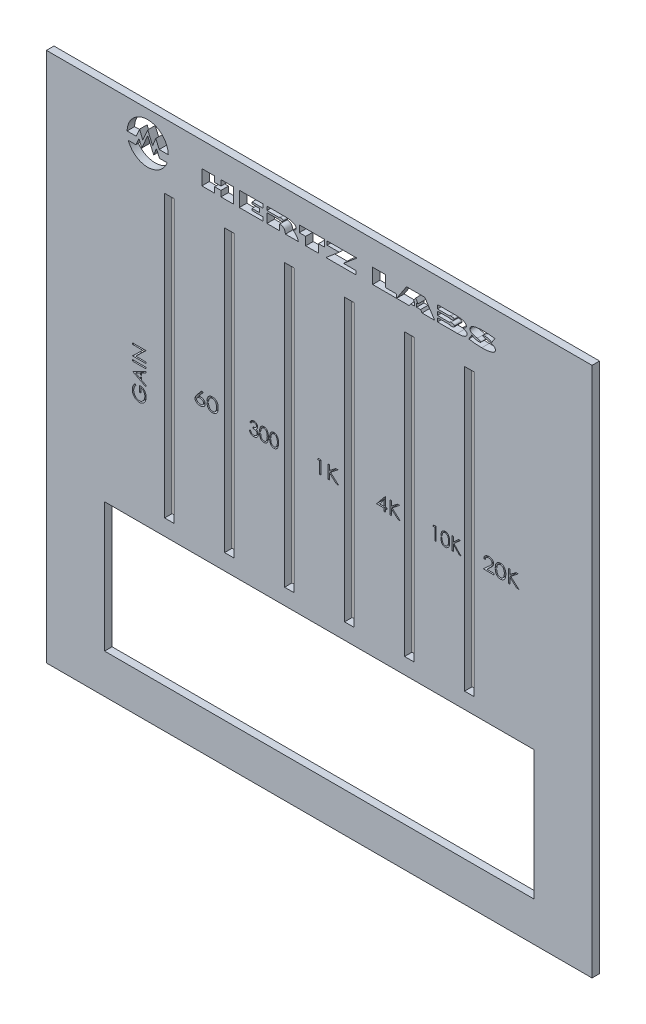
SolidWorks part; units mm, degrees
ref_plane "Front Plane" through (0, 0, 0) normal (0, 0, 1) x (1, 0, 0)
ref_plane "Top Plane" through (0, 0, 0) normal (0, 1, 0) x (1, 0, 0)
ref_plane "Right Plane" through (0, 0, 0) normal (1, 0, 0) x (0, 0, -1)
sketch "Sketch1" plane through (0, 0, 0) normal (0, 0, 1) x (1, 0, 0)
  line L1 (72.75, -70.75) -> (-72.75, -70.75)
  line L2 (72.75, -70.75) -> (72.75, 70.75)
  line L3 (72.75, 70.75) -> (-72.75, 70.75)
  line L4 (-72.75, -70.75) -> (-72.75, 70.75)
  line L5 (72.75, -70.75) -> (-72.75, 70.75) construction
  line L6 (72.75, 70.75) -> (-72.75, -70.75) construction
  point P0 (0, 0)
  dimension "D1" = 141.5
  dimension "D2" = 145.5
extrude "Boss-Extrude1" add sketch "Sketch1" along normal blind 2
sketch "Sketch2" plane through (0, 0, 2) normal (0, 0, 1) x (1, 0, 0)
  line L0 (-72.75, 70.75) -> (-72.75, -70.75) construction
  line L1 (-57.25, -60.25) -> (57.25, -60.25)
  line L2 (-57.25, -60.25) -> (-57.25, -25.75)
  line L3 (-57.25, -25.75) -> (57.25, -25.75)
  line L4 (57.25, -60.25) -> (57.25, -25.75)
  line L5 (72.75, -70.75) -> (72.75, 70.75) construction
  line L6 (-72.75, -70.75) -> (72.75, -70.75) construction
  line L7 (72.75, 70.75) -> (-72.75, 70.75) construction
  line L8 (-40, -3.9255) -> (-40, 57.7871) construction
  line L9 (-24, -3.9255) -> (-24, 57.7871) construction
  line L10 (-8, 57.7871) -> (-8, -3.9255) construction
  line L11 (0, -1.1) -> (0, 1.1) construction
  line L12 (-38.75, -21.5) -> (-41.25, -21.5)
  line L13 (-38.75, -21.5) -> (-38.75, 53.5)
  line L14 (-38.75, 53.5) -> (-41.25, 53.5)
  line L15 (-41.25, -21.5) -> (-41.25, 53.5)
  line L16 (-38.75, -21.5) -> (-41.25, 53.5) construction
  line L17 (-38.75, 53.5) -> (-41.25, -21.5) construction
  line L18 (-22.75, -21.5) -> (-25.25, -21.5)
  line L19 (-22.75, -21.5) -> (-22.75, 53.5)
  line L20 (-22.75, 53.5) -> (-25.25, 53.5)
  line L21 (-25.25, -21.5) -> (-25.25, 53.5)
  line L22 (-22.75, -21.5) -> (-25.25, 53.5) construction
  line L23 (-22.75, 53.5) -> (-25.25, -21.5) construction
  line L24 (-6.75, -21.5) -> (-9.25, -21.5)
  line L25 (-6.75, -21.5) -> (-6.75, 53.5)
  line L26 (-6.75, 53.5) -> (-9.25, 53.5)
  line L27 (-9.25, -21.5) -> (-9.25, 53.5)
  line L28 (-6.75, -21.5) -> (-9.25, 53.5) construction
  line L29 (-6.75, 53.5) -> (-9.25, -21.5) construction
  line L30 (6.75, 53.5) -> (9.25, 53.5)
  line L31 (9.25, -21.5) -> (9.25, 53.5)
  line L32 (6.75, -21.5) -> (9.25, -21.5)
  line L33 (6.75, -21.5) -> (6.75, 53.5)
  line L34 (22.75, 53.5) -> (25.25, 53.5)
  line L35 (25.25, -21.5) -> (25.25, 53.5)
  line L36 (22.75, -21.5) -> (25.25, -21.5)
  line L37 (22.75, -21.5) -> (22.75, 53.5)
  line L38 (38.75, 53.5) -> (41.25, 53.5)
  line L39 (41.25, -21.5) -> (41.25, 53.5)
  line L40 (38.75, -21.5) -> (41.25, -21.5)
  line L41 (38.75, -21.5) -> (38.75, 53.5)
  point P18 (-40, 16)
  point P23 (-24, 16)
  point P28 (-8, 16)
  dimension "D1" = 15.5
  dimension "D2" = 15.5
  dimension "D3" = 10.5
  dimension "D4" = 96.5
  dimension "D5" = 32.75
  dimension "D6" = 16
  dimension "D7" = 16
  dimension "D8" = 2.5
  dimension "D9" = 75
  dimension "D10" = 17.25
  dimension "D11" = 75
  dimension "D12" = 2.5
  dimension "D13" = 17.25
  dimension "D14" = 75
  dimension "D15" = 2.5
  dimension "D16" = 17.25
extrude "Cut-Extrude1" cut sketch "Sketch2" against normal blind 2
sketch "Sketch3" plane through (0, 0, 2) normal (0, 0, 1) x (1, 0, 0)
  line L0 (-46.537, 60.1618) -> (47.1821, 60.1618) construction
  text T0 "HERTZ LABS" font "Gill Sans Ultra Bold" height 4
extrude "Cut-Extrude2" cut sketch "Sketch3" against normal blind 2
sketch "Sketch4" plane through (0, 0, 2) normal (0, 0, 1) x (1, 0, 0)
  line L0 (-10.5679, 63.1618) -> (-13.9679, 63.1618)
  line L3 (-10.5679, 63.3118) -> (-10.5679, 62.5618) construction
  line L4 (-13.9679, 60.1618) -> (-13.9679, 64.1618) construction
  line L5 (-13.9679, 63.1618) -> (-13.9679, 62.6618)
  line L6 (-13.9679, 62.6618) -> (-10.5679, 62.6618)
  line L7 (-10.5679, 62.6618) -> (-10.5679, 63.1618)
  line L8 (25.4524, 60.7618) -> (25.4524, 61.7618)
  line L9 (27.0227, 60.7618) -> (24.3946, 60.7618) construction
  line L10 (25.0524, 61.7618) -> (26.3626, 61.7618) construction
  line L11 (25.4524, 61.7618) -> (25.9524, 61.7618)
  line L12 (25.9524, 61.7618) -> (25.9524, 60.7618)
  line L13 (25.9524, 60.7618) -> (25.4524, 60.7618)
  line L14 (34.9321, 63.1618) -> (31.5321, 63.1618)
  line L15 (34.9321, 63.3118) -> (34.9321, 62.5618) construction
  line L16 (31.5321, 60.1618) -> (31.5321, 64.1618) construction
  line L17 (31.5321, 63.1618) -> (31.5321, 62.6618)
  line L18 (31.5321, 62.6618) -> (34.9321, 62.6618)
  line L19 (34.9321, 62.6618) -> (34.9321, 63.1618)
  line L20 (34.9321, 61.6618) -> (31.5321, 61.6618)
  line L21 (34.9321, 61.8618) -> (34.9321, 61.0118) construction
  line L22 (31.5321, 61.6618) -> (31.5321, 61.1618)
  line L23 (31.5321, 61.1618) -> (34.9321, 61.1618)
  line L24 (34.9321, 61.1618) -> (34.9321, 61.6618)
  line L25 (31.5321, 64.1618) -> (36.2852, 64.1618) construction
  line L26 (36.8305, 60.1618) -> (31.5321, 60.1618) construction
  line L27 (-13.9679, 64.1618) -> (-8.957, 64.1618) construction
  dimension "D1" = 3.4
  dimension "D2" = 0.5
  dimension "D3" = 1
  dimension "D4" = 0.5
  dimension "D5" = 1
  dimension "D6" = 0.5
  dimension "D7" = 0.4
  dimension "D8" = 0.5
  dimension "D9" = 1
extrude "Boss-Extrude2" add sketch "Sketch4" against normal blind 2
sketch "Sketch5" plane through (0, 0, 2) normal (0, 0, 1) x (1, 0, 0)
  line L0 (-72.75, 70.75) -> (-72.75, -70.75) construction
  line L1 (72.75, 70.75) -> (-72.75, 70.75) construction
  line L2 (-51.2485, 62.8803) -> (-48.8137, 62.8803)
  line L3 (-48.8137, 62.8803) -> (-47.9043, 64.9798)
  line L4 (-47.9043, 64.9798) -> (-47.0636, 62.8542)
  line L5 (-47.0636, 62.8542) -> (-45.75, 65.8868)
  line L6 (-45.75, 69.0971) -> (-45.75, 56.4077) construction
  line L7 (-50.9225, 60.8803) -> (-48.8917, 60.8803)
  line L8 (-48.8917, 60.8803) -> (-48.0818, 62.75)
  line L9 (-48.0818, 62.75) -> (-47.3423, 60.8803)
  line L10 (-47.3423, 60.8803) -> (-45.75, 64.5564)
  line L11 (-40.5775, 60.8803) -> (-42.6083, 60.8803)
  line L12 (-42.6083, 60.8803) -> (-43.4182, 62.75)
  line L13 (-43.4182, 62.75) -> (-44.1577, 60.8803)
  line L14 (-44.1577, 60.8803) -> (-45.75, 64.5564)
  line L15 (-44.4364, 62.8542) -> (-45.75, 65.8868)
  line L16 (-43.5957, 64.9798) -> (-44.4364, 62.8542)
  line L17 (-42.6863, 62.8803) -> (-43.5957, 64.9798)
  line L18 (-40.2515, 62.8803) -> (-42.6863, 62.8803)
  arc A0 (-50.9225, 60.8803) -> (-40.5775, 60.8803) centre (-45.75, 62.75) ccw
  arc A1 (-40.2515, 62.8803) -> (-51.2485, 62.8803) centre (-45.75, 62.75) ccw
  dimension "D1" = 11
  dimension "D2" = 27
  dimension "D3" = 8
  dimension "D4" = 2
  dimension "D5" = 0
  dimension "D6" = 0
  dimension "D7" = 360
extrude "Cut-Extrude3" cut sketch "Sketch5" against normal blind 2
sketch "Sketch7" plane through (0, 0, 2) normal (0, 0, 1) x (1, 0, 0)
  line L0 (-34.0617, 9.25) -> (-26.7208, 9.25) construction
  line L1 (-19.38, 9.25) -> (-10.6797, 9.25) construction
  line L2 (-2.931, 9.25) -> (5.2255, 9.25) construction
  line L3 (13.9257, 9.25) -> (21.6744, 9.25) construction
  line L4 (29.0152, 9.25) -> (37.8514, 9.25) construction
  line L5 (43.561, 9.25) -> (56.6702, 9.25) construction
  line L6 (-46.25, 1.5274) -> (-46.25, 38.0957) construction
  line L7 (-41.25, 53.5) -> (-41.25, -21.5) construction
  line L8 (57.25, -25.75) -> (-57.25, -25.75) construction
  text T0 "60" font "Century Gothic" height 3.5
  text T1 "300" font "Century Gothic" height 3.5
  text T2 "1K" font "Century Gothic" height 3.5
  text T3 "4K" font "Century Gothic" height 3.5
  text T4 "10K" font "Century Gothic" height 3.5
  text T5 "20K" font "Century Gothic" height 3.5
  text T6 "GAIN" font "Century Gothic" height 3.5
  dimension "D1" = 5
  dimension "D2" = 35
extrude "Cut-Extrude4" cut sketch "Sketch7" against normal blind 2
sketch "Sketch8" plane through (0, 0, 2) normal (0, 0, 1) x (1, 0, 0)
  line L0 (-47.7308, 8.3128) -> (-47.3718, 8.3128)
  line L1 (-47.7308, 7.4399) -> (-47.7308, 8.7384) construction
  line L2 (-47.3718, 8.9172) -> (-47.3718, 7.2556) construction
  line L3 (-47.3718, 8.3128) -> (-47.3718, 7.907)
  line L4 (-47.3718, 7.907) -> (-47.7308, 7.907)
  line L5 (-47.7308, 7.907) -> (-47.7308, 8.3128)
  line L6 (-15.9287, 11.1102) -> (-15.6148, 11.1102)
  line L7 (-15.6148, 11.1102) -> (-15.6111, 10.7758)
  line L8 (-15.6111, 10.7758) -> (-15.9258, 10.7758)
  line L9 (-15.9258, 10.7758) -> (-15.9287, 11.1102)
  line L10 (-13.2364, 11.1102) -> (-12.9225, 11.1102)
  line L11 (-12.9225, 11.1102) -> (-12.92, 10.8036)
  line L12 (-12.92, 10.8036) -> (-13.2345, 10.8036)
  line L13 (-13.2345, 10.8036) -> (-13.2364, 11.1102)
  line L14 (-29.9472, 11.2049) -> (-29.4983, 11.2049)
  line L15 (-29.4983, 11.2049) -> (-29.5006, 10.8534)
  line L16 (-29.5006, 10.8534) -> (-29.9495, 10.8534)
  line L17 (-29.9495, 10.8534) -> (-29.9472, 11.2049)
  line L18 (32.4311, 11.326) -> (32.7462, 11.326)
  line L19 (32.7462, 11.326) -> (32.7363, 10.943)
  line L20 (32.7363, 10.943) -> (32.4223, 10.943)
  line L21 (32.4223, 10.943) -> (32.4311, 11.326)
  line L22 (46.9306, 11.2049) -> (47.3344, 11.2049)
  line L23 (47.3344, 11.2049) -> (47.3323, 10.8611)
  line L24 (47.3323, 10.8611) -> (46.9283, 10.8611)
  line L25 (46.9283, 10.8611) -> (46.9306, 11.2049)
  spline S0 degree 3 poles (-15.9297, 10.9986) (-15.9294, 11.0547) (-15.9287, 11.1637) (-15.9217, 11.3224) (-15.9099, 11.4714) (-15.8937, 11.6106) (-15.8741, 11.7399) (-15.8479, 11.8591) (-15.8181, 11.9688) (-15.7835, 12.0693) (-15.7445, 12.1618) (-15.7021, 12.2483) (-15.6545, 12.3284) (-15.6046, 12.4035) (-15.5502, 12.4724) (-15.4929, 12.5361) (-15.4304, 12.593) (-15.365, 12.6448) (-15.296, 12.6903) (-15.2253, 12.7303) (-15.1526, 12.7645) (-15.0775, 12.7914) (-15.0008, 12.8136) (-14.9222, 12.8288) (-14.8416, 12.8384) (-14.7871, 12.8393) (-14.7595, 12.8397) knots 0 0 0 0 0.068595 0.133246 0.194313 0.251279 0.304513 0.354235 0.400481 0.443411 0.484015 0.523252 0.561042 0.5979 0.633518 0.668314 0.702496 0.736685 0.770293 0.803437 0.835913 0.86846 0.900847 0.933467 0.966258 1 1 1 1 construction
  spline S1 degree 3 poles (-14.749, 12.4808) (-14.7877, 12.4787) (-14.8652, 12.4747) (-14.9797, 12.446) (-15.0894, 12.396) (-15.1766, 12.341) (-15.2435, 12.2887) (-15.2906, 12.2433) (-15.3347, 12.1936) (-15.3754, 12.1392) (-15.4135, 12.0808) (-15.4485, 12.0178) (-15.48, 11.95) (-15.5091, 11.8773) (-15.5346, 11.7978) (-15.5557, 11.71) (-15.5752, 11.6135) (-15.589, 11.5078) (-15.6013, 11.3935) (-15.6091, 11.2702) (-15.6153, 11.1382) (-15.6155, 11.047) (-15.6156, 11) knots 0 0 0 0 0.060387 0.120883 0.182755 0.247811 0.281299 0.315088 0.349702 0.384857 0.420966 0.458511 0.497175 0.537602 0.580503 0.627468 0.678388 0.733983 0.793747 0.857714 0.926698 1 1 1 1 construction
  spline S2 degree 3 poles (-15.6156, 11) (-15.6155, 10.9533) (-15.6153, 10.8625) (-15.6092, 10.7307) (-15.601, 10.6077) (-15.5903, 10.4935) (-15.5745, 10.3883) (-15.5568, 10.2915) (-15.5353, 10.2037) (-15.5098, 10.1241) (-15.4807, 10.0514) (-15.449, 9.9838) (-15.415, 9.9205) (-15.3768, 9.8619) (-15.3353, 9.808) (-15.2913, 9.7578) (-15.2433, 9.713) (-15.1768, 9.6593) (-15.089, 9.6038) (-14.9784, 9.5554) (-14.8647, 9.525) (-14.7875, 9.5212) (-14.749, 9.5192) knots 0 0 0 0 0.072951 0.141584 0.205926 0.265301 0.320597 0.371817 0.41879 0.461699 0.502134 0.540804 0.578181 0.614297 0.649678 0.684299 0.718359 0.752081 0.817652 0.879722 0.939966 1 1 1 1 construction
  spline S3 degree 3 poles (-14.7595, 9.1603) (-14.7871, 9.1607) (-14.8416, 9.1616) (-14.9222, 9.1712) (-15.0005, 9.1865) (-15.0768, 9.2079) (-15.1515, 9.2341) (-15.2236, 9.2682) (-15.2939, 9.3076) (-15.3622, 9.3524) (-15.4272, 9.4037) (-15.4893, 9.4605) (-15.5469, 9.5241) (-15.6006, 9.5936) (-15.6515, 9.6682) (-15.6984, 9.7492) (-15.7418, 9.836) (-15.7814, 9.9293) (-15.8166, 10.0305) (-15.8476, 10.1406) (-15.8721, 10.2608) (-15.8931, 10.3899) (-15.9101, 10.5285) (-15.9216, 10.6769) (-15.9288, 10.8347) (-15.9294, 10.943) (-15.9297, 10.9986) knots 0 0 0 0 0.033787 0.066622 0.099285 0.131361 0.163585 0.196104 0.228902 0.262158 0.295991 0.330218 0.36506 0.400951 0.43762 0.475708 0.515381 0.556414 0.599765 0.646424 0.696431 0.749782 0.806573 0.867436 0.931887 1 1 1 1 construction
  spline S4 degree 3 poles (-13.2374, 10.9986) (-13.2371, 11.0547) (-13.2364, 11.1637) (-13.2294, 11.3224) (-13.2176, 11.4714) (-13.2014, 11.6106) (-13.1818, 11.7399) (-13.1556, 11.8591) (-13.1258, 11.9688) (-13.0912, 12.0693) (-13.0522, 12.1618) (-13.0098, 12.2483) (-12.9622, 12.3284) (-12.9123, 12.4035) (-12.8578, 12.4724) (-12.8005, 12.5361) (-12.7381, 12.593) (-12.6727, 12.6448) (-12.6037, 12.6903) (-12.533, 12.7303) (-12.4603, 12.7645) (-12.3852, 12.7914) (-12.3085, 12.8136) (-12.2299, 12.8288) (-12.1493, 12.8384) (-12.0948, 12.8393) (-12.0672, 12.8397) knots 0 0 0 0 0.068595 0.133246 0.194313 0.251279 0.304513 0.354235 0.400481 0.443411 0.484015 0.523252 0.561042 0.5979 0.633518 0.668314 0.702496 0.736685 0.770293 0.803437 0.835913 0.86846 0.900847 0.933467 0.966258 1 1 1 1 construction
  spline S5 degree 3 poles (-12.0567, 12.4808) (-12.0954, 12.4787) (-12.1729, 12.4747) (-12.2874, 12.446) (-12.3971, 12.396) (-12.4843, 12.341) (-12.5512, 12.2887) (-12.5983, 12.2433) (-12.6424, 12.1936) (-12.6831, 12.1392) (-12.7212, 12.0808) (-12.7561, 12.0178) (-12.7877, 11.95) (-12.8167, 11.8773) (-12.8423, 11.7978) (-12.8634, 11.71) (-12.8829, 11.6135) (-12.8967, 11.5078) (-12.909, 11.3935) (-12.9168, 11.2702) (-12.923, 11.1382) (-12.9232, 11.047) (-12.9233, 11) knots 0 0 0 0 0.060387 0.120883 0.182755 0.247811 0.281299 0.315088 0.349702 0.384857 0.420966 0.458511 0.497175 0.537602 0.580503 0.627468 0.678388 0.733983 0.793747 0.857714 0.926698 1 1 1 1 construction
  spline S6 degree 3 poles (-12.9233, 11) (-12.9232, 10.9533) (-12.9229, 10.8625) (-12.9169, 10.7307) (-12.9086, 10.6077) (-12.898, 10.4935) (-12.8822, 10.3883) (-12.8645, 10.2915) (-12.8429, 10.2037) (-12.8174, 10.1241) (-12.7884, 10.0514) (-12.7567, 9.9838) (-12.7226, 9.9205) (-12.6845, 9.8619) (-12.643, 9.808) (-12.599, 9.7578) (-12.551, 9.713) (-12.4845, 9.6593) (-12.3967, 9.6038) (-12.286, 9.5554) (-12.1724, 9.525) (-12.0952, 9.5212) (-12.0567, 9.5192) knots 0 0 0 0 0.072951 0.141584 0.205926 0.265301 0.320597 0.371817 0.41879 0.461699 0.502134 0.540804 0.578181 0.614297 0.649678 0.684299 0.718359 0.752081 0.817652 0.879722 0.939966 1 1 1 1 construction
  spline S7 degree 3 poles (-12.0672, 9.1603) (-12.0948, 9.1607) (-12.1493, 9.1616) (-12.2299, 9.1712) (-12.3082, 9.1865) (-12.3845, 9.2079) (-12.4592, 9.2341) (-12.5313, 9.2682) (-12.6016, 9.3076) (-12.6699, 9.3524) (-12.7349, 9.4037) (-12.797, 9.4605) (-12.8546, 9.5241) (-12.9083, 9.5936) (-12.9592, 9.6682) (-13.0061, 9.7492) (-13.0495, 9.836) (-13.0891, 9.9293) (-13.1243, 10.0305) (-13.1553, 10.1406) (-13.1798, 10.2608) (-13.2008, 10.3899) (-13.2177, 10.5285) (-13.2293, 10.6769) (-13.2364, 10.8347) (-13.2371, 10.943) (-13.2374, 10.9986) knots 0 0 0 0 0.033787 0.066622 0.099285 0.131361 0.163585 0.196104 0.228902 0.262158 0.295991 0.330218 0.36506 0.400951 0.43762 0.475708 0.515381 0.556414 0.599765 0.646424 0.696431 0.749782 0.806573 0.867436 0.931887 1 1 1 1 construction
  spline S8 degree 3 poles (-29.9516, 10.9986) (-29.9512, 11.0547) (-29.9503, 11.1637) (-29.9408, 11.3225) (-29.9265, 11.4716) (-29.9062, 11.6108) (-29.8808, 11.7402) (-29.8484, 11.8596) (-29.811, 11.9696) (-29.7662, 12.0697) (-29.7167, 12.1623) (-29.6629, 12.2488) (-29.6034, 12.329) (-29.54, 12.4043) (-29.4708, 12.4729) (-29.3979, 12.5369) (-29.3187, 12.5931) (-29.2363, 12.6455) (-29.1493, 12.6904) (-29.0603, 12.7307) (-28.9686, 12.7647) (-28.874, 12.7916) (-28.7771, 12.8136) (-28.6778, 12.8289) (-28.5759, 12.8383) (-28.5071, 12.8393) (-28.4722, 12.8397) knots 0 0 0 0 0.062652 0.121739 0.177604 0.229836 0.278824 0.324793 0.367881 0.408429 0.447198 0.485074 0.522035 0.558698 0.594873 0.630771 0.666849 0.703204 0.739747 0.776081 0.812252 0.84893 0.885848 0.923096 0.961095 1 1 1 1 construction
  spline S9 degree 3 poles (-28.4582, 12.4808) (-28.5051, 12.4788) (-28.598, 12.4749) (-28.7355, 12.446) (-28.8677, 12.3969) (-28.9731, 12.3416) (-29.0534, 12.2888) (-29.1103, 12.2437) (-29.1636, 12.1941) (-29.2126, 12.1394) (-29.2596, 12.0817) (-29.3003, 12.0177) (-29.3395, 11.9506) (-29.3738, 11.8775) (-29.4055, 11.7983) (-29.4305, 11.7102) (-29.4534, 11.6137) (-29.4709, 11.5079) (-29.4861, 11.3936) (-29.4951, 11.2703) (-29.5018, 11.1382) (-29.5025, 11.047) (-29.5029, 11) knots 0 0 0 0 0.06843 0.135704 0.204056 0.273826 0.309041 0.344276 0.379774 0.415293 0.451486 0.488217 0.52598 0.56491 0.605982 0.650476 0.698495 0.750792 0.806886 0.866807 0.931388 1 1 1 1 construction
  spline S10 degree 3 poles (-29.5029, 11) (-29.5025, 10.9532) (-29.5018, 10.8625) (-29.4952, 10.7307) (-29.4859, 10.6076) (-29.4718, 10.4934) (-29.4539, 10.388) (-29.4314, 10.2914) (-29.406, 10.2033) (-29.3754, 10.1237) (-29.3407, 10.0511) (-29.3028, 9.9832) (-29.2607, 9.9203) (-29.2149, 9.8615) (-29.1649, 9.8077) (-29.1117, 9.7574) (-29.0538, 9.7127) (-28.9731, 9.6588) (-28.8669, 9.6031) (-28.7338, 9.5551) (-28.5972, 9.525) (-28.5046, 9.5211) (-28.4582, 9.5192) knots 0 0 0 0 0.068273 0.132516 0.192779 0.248494 0.300456 0.348809 0.393305 0.434254 0.473186 0.510782 0.547702 0.583685 0.619435 0.654935 0.690439 0.726129 0.796665 0.864903 0.932249 1 1 1 1 construction
  spline S11 degree 3 poles (-28.4722, 9.1603) (-28.5071, 9.1607) (-28.5759, 9.1617) (-28.6778, 9.171) (-28.7768, 9.1865) (-28.8732, 9.2077) (-28.9675, 9.2339) (-29.0586, 9.268) (-29.1472, 9.3075) (-29.2335, 9.3518) (-29.3155, 9.4033) (-29.3937, 9.4599) (-29.4669, 9.5235) (-29.5353, 9.5929) (-29.5997, 9.6675) (-29.6586, 9.7487) (-29.7132, 9.8355) (-29.7634, 9.9288) (-29.8089, 10.0297) (-29.8472, 10.1403) (-29.879, 10.2604) (-29.9055, 10.3896) (-29.9267, 10.5284) (-29.9408, 10.6768) (-29.9503, 10.8346) (-29.9512, 10.943) (-29.9516, 10.9986) knots 0 0 0 0 0.038955 0.077002 0.114298 0.150951 0.187352 0.223569 0.259604 0.295841 0.331882 0.367795 0.403739 0.440145 0.476656 0.513875 0.55216 0.591332 0.632276 0.675753 0.722032 0.771134 0.823213 0.87889 0.937791 1 1 1 1 construction
  spline S12 degree 3 poles (32.4219, 10.9986) (32.4223, 11.0547) (32.4229, 11.1637) (32.43, 11.3224) (32.4418, 11.4714) (32.4579, 11.6106) (32.4775, 11.7399) (32.5038, 11.8591) (32.5336, 11.9688) (32.5681, 12.0693) (32.6071, 12.1618) (32.6496, 12.2483) (32.6971, 12.3284) (32.7471, 12.4035) (32.8015, 12.4724) (32.8588, 12.5361) (32.9212, 12.593) (32.9866, 12.6448) (33.0557, 12.6903) (33.1263, 12.7303) (33.1991, 12.7645) (33.2741, 12.7914) (33.3508, 12.8136) (33.4294, 12.8288) (33.5101, 12.8384) (33.5645, 12.8393) (33.5921, 12.8397) knots 0 0 0 0 0.068595 0.133246 0.194313 0.251279 0.304513 0.354235 0.400481 0.443411 0.484015 0.523252 0.561042 0.5979 0.633518 0.668314 0.702496 0.736685 0.770293 0.803437 0.835913 0.86846 0.900847 0.933467 0.966258 1 1 1 1 construction
  spline S13 degree 3 poles (33.6026, 12.4808) (33.5639, 12.4787) (33.4864, 12.4747) (33.372, 12.446) (33.2623, 12.396) (33.175, 12.341) (33.1082, 12.2887) (33.0611, 12.2433) (33.0169, 12.1936) (32.9763, 12.1392) (32.9382, 12.0808) (32.9032, 12.0178) (32.8717, 11.95) (32.8426, 11.8773) (32.817, 11.7978) (32.7959, 11.71) (32.7764, 11.6135) (32.7627, 11.5078) (32.7504, 11.3935) (32.7425, 11.2702) (32.7364, 11.1382) (32.7362, 11.047) (32.736, 11) knots 0 0 0 0 0.060387 0.120883 0.182755 0.247811 0.281299 0.315088 0.349702 0.384857 0.420966 0.458511 0.497175 0.537602 0.580503 0.627468 0.678388 0.733983 0.793747 0.857714 0.926698 1 1 1 1 construction
  spline S14 degree 3 poles (32.736, 11) (32.7362, 10.9533) (32.7364, 10.8625) (32.7425, 10.7307) (32.7507, 10.6077) (32.7613, 10.4935) (32.7771, 10.3883) (32.7949, 10.2915) (32.8164, 10.2037) (32.8419, 10.1241) (32.8709, 10.0514) (32.9026, 9.9838) (32.9367, 9.9205) (32.9748, 9.8619) (33.0163, 9.808) (33.0603, 9.7578) (33.1084, 9.713) (33.1749, 9.6593) (33.2627, 9.6038) (33.3733, 9.5554) (33.487, 9.525) (33.5641, 9.5212) (33.6026, 9.5192) knots 0 0 0 0 0.072951 0.141584 0.205926 0.265301 0.320597 0.371817 0.41879 0.461699 0.502134 0.540804 0.578181 0.614297 0.649678 0.684299 0.718359 0.752081 0.817652 0.879722 0.939966 1 1 1 1 construction
  spline S15 degree 3 poles (33.5921, 9.1603) (33.5645, 9.1607) (33.5101, 9.1616) (33.4294, 9.1712) (33.3511, 9.1865) (33.2748, 9.2079) (33.2001, 9.2341) (33.128, 9.2682) (33.0578, 9.3076) (32.9895, 9.3524) (32.9245, 9.4037) (32.8624, 9.4605) (32.8047, 9.5241) (32.7511, 9.5936) (32.7001, 9.6682) (32.6532, 9.7492) (32.6099, 9.836) (32.5702, 9.9293) (32.5351, 10.0305) (32.504, 10.1406) (32.4795, 10.2608) (32.4585, 10.3899) (32.4416, 10.5285) (32.43, 10.6769) (32.4229, 10.8347) (32.4223, 10.943) (32.4219, 10.9986) knots 0 0 0 0 0.033787 0.066622 0.099285 0.131361 0.163585 0.196104 0.228902 0.262158 0.295991 0.330218 0.36506 0.400951 0.43762 0.475708 0.515381 0.556414 0.599765 0.646424 0.696431 0.749782 0.806573 0.867436 0.931887 1 1 1 1 construction
  spline S16 degree 3 poles (46.9264, 10.9986) (46.9268, 11.0547) (46.9278, 11.1637) (46.9367, 11.3225) (46.9491, 11.4716) (46.9691, 11.6107) (46.9932, 11.74) (47.0232, 11.8595) (47.0587, 11.9693) (47.1004, 12.0697) (47.1473, 12.162) (47.1974, 12.2487) (47.2535, 12.329) (47.3134, 12.404) (47.3783, 12.4729) (47.4469, 12.5366) (47.5212, 12.5931) (47.5986, 12.6452) (47.6803, 12.6905) (47.7643, 12.7306) (47.8507, 12.7644) (47.9396, 12.7917) (48.0307, 12.8136) (48.1242, 12.8289) (48.22, 12.8383) (48.2846, 12.8393) (48.3174, 12.8397) knots 0 0 0 0 0.064278 0.124884 0.18215 0.2357 0.285857 0.332815 0.376766 0.417944 0.457225 0.495391 0.532533 0.569294 0.60529 0.640921 0.676433 0.712158 0.747766 0.783342 0.818699 0.85402 0.889809 0.925909 0.962494 1 1 1 1 construction
  spline S17 degree 3 poles (48.33, 12.4808) (48.2852, 12.4788) (48.1962, 12.4748) (48.0645, 12.446) (47.938, 12.3968) (47.8372, 12.3416) (47.7607, 12.2885) (47.7058, 12.244) (47.6555, 12.1935) (47.6076, 12.1398) (47.5639, 12.0811) (47.5242, 12.0177) (47.4866, 11.9505) (47.4537, 11.8774) (47.4236, 11.7981) (47.3988, 11.7103) (47.3779, 11.6135) (47.3607, 11.5079) (47.3466, 11.3936) (47.3369, 11.2703) (47.3315, 11.1382) (47.3307, 11.047) (47.3302, 11) knots 0 0 0 0 0.066462 0.132148 0.199048 0.267542 0.302199 0.337214 0.372307 0.407957 0.443911 0.480881 0.518937 0.558228 0.59974 0.644883 0.693554 0.74667 0.803662 0.864588 0.930237 1 1 1 1 construction
  spline S18 degree 3 poles (47.3302, 11) (47.3307, 10.9533) (47.3315, 10.8625) (47.3369, 10.7306) (47.3468, 10.6076) (47.3597, 10.4934) (47.3774, 10.3882) (47.3979, 10.2913) (47.4231, 10.2035) (47.452, 10.1238) (47.4854, 10.0511) (47.522, 9.9835) (47.5617, 9.92) (47.6063, 9.862) (47.6533, 9.8074) (47.7045, 9.7575) (47.7602, 9.7129) (47.8372, 9.6588) (47.9387, 9.6032) (48.066, 9.5552) (48.1968, 9.5249) (48.2854, 9.5211) (48.33, 9.5192) knots 0 0 0 0 0.069416 0.134719 0.195991 0.252597 0.305371 0.354381 0.399525 0.440916 0.480206 0.518096 0.555067 0.591229 0.626651 0.661991 0.697275 0.732416 0.801686 0.868462 0.933883 1 1 1 1 construction
  spline S19 degree 3 poles (48.3174, 9.1603) (48.2846, 9.1607) (48.22, 9.1617) (48.1242, 9.1711) (48.031, 9.1865) (47.9402, 9.2077) (47.8515, 9.2339) (47.7659, 9.2682) (47.6824, 9.3073) (47.6015, 9.352) (47.5244, 9.4035) (47.4505, 9.46) (47.3815, 9.5234) (47.3181, 9.5934) (47.2571, 9.6675) (47.2018, 9.7488) (47.1508, 9.8358) (47.1032, 9.9289) (47.0609, 10.03) (47.0244, 10.1404) (46.995, 10.2606) (46.9696, 10.3897) (46.9501, 10.5285) (46.9364, 10.6768) (46.9279, 10.8347) (46.9269, 10.943) (46.9264, 10.9986) knots 0 0 0 0 0.037555 0.074188 0.110335 0.145848 0.181136 0.21629 0.251555 0.286845 0.322244 0.357803 0.39348 0.429537 0.466137 0.503548 0.542131 0.581824 0.623406 0.667753 0.715032 0.765305 0.818659 0.875757 0.936174 1 1 1 1 construction
extrude "Boss-Extrude3" add sketch "Sketch8" against normal blind 2
